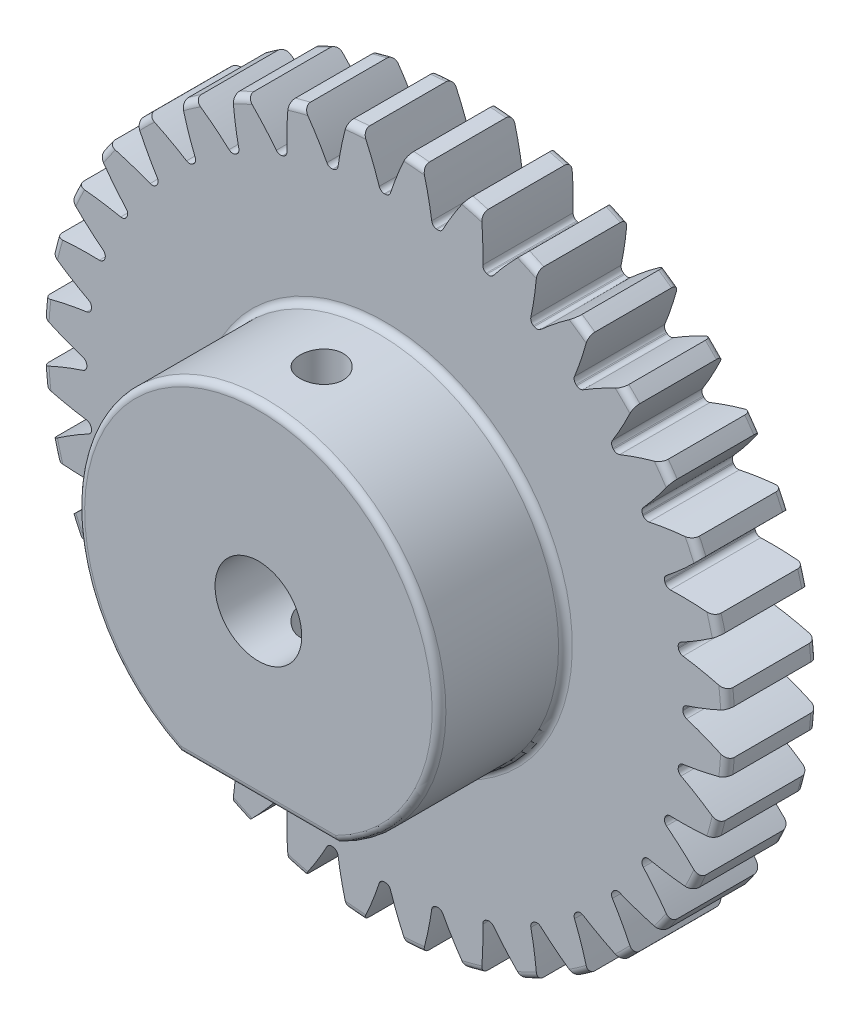
SolidWorks part; units mm, degrees
ref_plane "Front Plane" through (0, 0, 0) normal (0, 0, 1) x (1, 0, 0)
ref_plane "Top Plane" through (0, 0, 0) normal (0, 1, 0) x (1, 0, 0)
ref_plane "Right Plane" through (0, 0, 0) normal (1, 0, 0) x (0, 0, -1)
sketch "Sketch1" plane through (0, 0, 0) normal (0, 0, 1) x (1, 0, 0)
  line L0 (-457.2, 0) -> (457.2, 0) construction
  circle A0 centre (0, 0) radius 24.13 construction
  circle A1 centre (0, 0) radius 22.86 construction
  circle A2 centre (0, 0) radius 20.955 construction
  circle A3 centre (0, 0) radius 12.7 construction
  circle A4 centre (0, 0) radius 3.048 construction
  dimension "D2" = 1.27
  dimension "D3" = 3.175
  dimension "D1" = 3.175
sketch "Sketch2" plane through (0, 0, 0) normal (1, 0, 0) x (0, 0, -1)
  line L0 (0, 0) -> (-6.35, 0) construction
  line L1 (-6.35, 0) -> (-15.24, 0) construction
  dimension "Overall Width" = 15.24
  dimension "Face Width" = 6.35
sketch "Sketch4" plane through (0, 0, 0) normal (1, 0, 0) x (0, 0, -1)
  line L0 (-15.24, 3.048) -> (-15.24, 12.7)
  line L1 (-15.24, 12.7) -> (-6.35, 12.7)
  line L2 (-6.35, 12.7) -> (-6.35, 24.13)
  line L3 (-6.35, 24.13) -> (0, 24.13)
  line L4 (0, 24.13) -> (0, 3.048)
  line L5 (-6.35, 12.7) -> (-6.35, 0) construction
  line L6 (0, 24.13) -> (0, -24.13) construction
  line L7 (-6.35, 12.7) -> (0, 12.7) construction
  line L12 (-15.24, 3.048) -> (0, 3.048)
revolve "Revolve1" add sketch "Sketch4" angle 360 about L1
fillet "Fillet2" radius 0.4826 2 edges at (0, 24.13, 6.35) (0, 24.13, 0)
sketch "Sketch7" plane through (0, 0, 6.35) normal (0, 0, 1) x (1, 0, 0)
  line L0 (0, 0) -> (0, 24.13) construction
  line L1 (0.9971, 22.8382) -> (1.5125, 24.0825) construction
  line L3 (2.1031, 24.0382) -> (1.9924, 22.773) construction
  line L4 (1.9924, 22.773) -> (1.8263, 20.8753) construction
  line L5 (0, 0) -> (1.8263, 20.8753) construction
  line L6 (0.9971, 22.8382) -> (0, 0) construction
  line L7 (0.9971, 22.8382) -> (1.0525, 24.107) construction
  line L8 (0.9971, 22.8382) -> (0, 0) construction
  circle A0 centre (0, 0) radius 24.13 construction
  arc A1 (-0.0338, 20.955) -> (0.0338, 20.955) centre (0, 0) cw
  circle A2 centre (0, 0) radius 20.955 construction
  arc A3 (-0.9971, 22.8382) -> (0.9971, 22.8382) centre (0, 0) cw construction
  circle A4 centre (0, 0) radius 22.86 construction
  arc A5 (2.6498, 23.9841) -> (1.5553, 24.0798) centre (0, 0) ccw construction
  arc A6 (0.9971, 22.8382) -> (2.9838, 22.6644) centre (0, 0) cw construction
  arc A7 (-1.5553, 24.0798) -> (1.5553, 24.0798) centre (0, 0) cw
  arc A8 (0.3964, 21.2172) -> (1.5553, 24.0798) centre (22.117, 14.0901) cw
  arc A9 (-0.3964, 21.2172) -> (-1.5553, 24.0798) centre (-22.117, 14.0901) ccw
  arc A10 (-0.0338, 20.955) -> (-0.3964, 21.2172) centre (-0.0344, 21.336) cw
  arc A11 (0.0338, 20.955) -> (0.3964, 21.2172) centre (0.0344, 21.336) ccw
  point P26 (-0.3114, 20.9527)
  point P29 (0.3114, 20.9527)
  dimension "D4" = 0.381
  dimension "D5" = 22.86
  dimension "D3" = 20
  dimension "D1" = 3.9898
  dimension "D2" = 1.9949
extrude "Cut-Extrude2" cut sketch "Sketch7" against normal through all
pattern_circular "CirPattern1" count 36 over 360 about axis through (0, 0, 0) along (0, 0, 1) of "Cut-Extrude2"
sketch "Sketch8" plane through (0, 0, 15.24) normal (0, 0, 1) x (1, 0, 0)
  line L4 (5.5358, -11.43) -> (-5.5358, -11.43)
  circle A4 centre (0, 0) radius 12.7 construction
  arc A5 (-5.5358, -11.43) -> (5.5358, -11.43) centre (0, 0) ccw
  point P5 (-0.1952, -7.62)
  dimension "D1" = 11.43
extrude "Cut-Extrude3" cut sketch "Sketch8" against normal up to surface (8.89 mm away) up to face at (0, 0, 6.35)
fillet "Fillet4" radius 0.4826 4 edges at (0, 12.7, 6.35) (0, 12.7, 15.24) (0, -11.43, 15.24) (0, -11.43, 6.35)
sketch "Sketch9" plane through (0, -11.43, 0) normal (0, -1, 0) x (1, 0, 0)
  line L2 (-5.5358, 10.795) -> (5.5358, 10.795) construction
  line L3 (-5.5358, 6.8326) -> (-5.5358, 14.7574) construction
  line L4 (5.5358, 6.8326) -> (5.5358, 14.7574) construction
  line L5 (0, 14.7574) -> (0, 6.8326) construction
  line L6 (5.5358, 14.7574) -> (-5.5358, 14.7574) construction
  line L7 (-5.5358, 6.8326) -> (5.5358, 6.8326) construction
  point P12 (0, 10.795)
hole_wizard "Tap Drill for #4 Helicoil1" positions "Sketch10" profile "Sketch11" hole size "#4-40" standard "ANSI Inch" end condition through all
sketch "Sketch10" plane through (0, -11.43, 0) normal (0, -1, 0) x (-1, 0, 0)
  point P0 (0, -10.795)
sketch "Sketch11" plane through (0, -11.43, 10.795) normal (1, 0, 0) x (0, 0, -1)
  line L0 (0, 0) -> (0, 35.543)
  line L1 (0, 35.543) -> (1.524, 35.543)
  line L2 (1.524, 35.543) -> (1.524, 0)
  line L5 (1.524, 0) -> (0, 0)
  line L11 (0, -6.35) -> (0, 107.95) construction
  dimension "Thru Hole Dia." = 3.048
  dimension "Thru Hole Depth" = 35.543
equation "\"D1@Sketch1\"=2.5*(\"Pitch Dia.@Sketch1\"/\"Number of Teeth@Sketch1\")"
equation "\"D1@CirPattern1\"=\"Number of Teeth@Sketch1\""
equation "\"D1@Fillet2\"=\"OD@Sketch1\"*.01"
equation "\"D1@Sketch7\"=3.14159*(\"Pitch Dia.@Sketch1\"/\"Number of Teeth@Sketch1\")"
equation "\"D2@Sketch7\"=\"D1@Sketch7\"/2"
equation "\"D4@Sketch7\"=\"D1@Sketch7\"*.0955"
equation "\"D5@Sketch7\"=\"Pitch Dia.@Sketch1\"/2"
